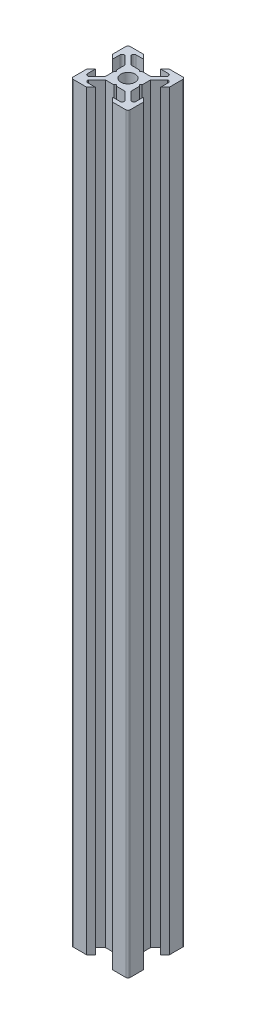
SolidWorks part; units mm, degrees
ref_plane "Face" through (0, 0, 0) normal (0, 0, 1) x (1, 0, 0)
ref_plane "Dessus" through (0, 0, 0) normal (0, 1, 0) x (1, 0, 0)
ref_plane "Droite" through (0, 0, 0) normal (1, 0, 0) x (0, 0, -1)
sketch "Esquisse1" plane through (0, 0, 0) normal (0, 1, 0) x (1, 0, 0)
  line L0 (0, 0) -> (0, 10) construction
  line L1 (0, 0) -> (-10, 0) construction
  line L2 (-10, 0) -> (-10, 10) construction
  line L3 (-10, 10) -> (0, 10) construction
  line L4 (0, 4) -> (-0.5, 4.5)
  line L5 (-0.5, 4.5) -> (-3.4393, 4.5)
  line L6 (-3.4393, 4.5) -> (-6.4393, 7.5)
  line L7 (-6.4393, 7.5) -> (-6.4393, 8.5)
  line L8 (-6.4393, 8.5) -> (-3, 8.5)
  line L9 (-3, 8.5) -> (-4.5, 10)
  line L10 (-4.5, 10) -> (-10, 10)
  line L11 (0, 0) -> (-10, 10) construction
  line L12 (-10, 4.5) -> (-10, 10)
  line L13 (-8.5, 3) -> (-10, 4.5)
  line L14 (-8.5, 6.4393) -> (-8.5, 3)
  line L15 (-7.5, 6.4393) -> (-8.5, 6.4393)
  line L16 (-4.5, 3.4393) -> (-7.5, 6.4393)
  line L17 (-4.5, 0.5) -> (-4.5, 3.4393)
  line L18 (-4, 0) -> (-4.5, 0.5)
  line L19 (0, -4) -> (-0.5, -4.5)
  line L20 (-0.5, -4.5) -> (-3.4393, -4.5)
  line L21 (-4, 0) -> (-4.5, -0.5)
  line L22 (-4.5, -0.5) -> (-4.5, -3.4393)
  line L23 (-4.5, -3.4393) -> (-7.5, -6.4393)
  line L24 (-3.4393, -4.5) -> (-6.4393, -7.5)
  line L25 (-3, -8.5) -> (-4.5, -10)
  line L26 (-6.4393, -8.5) -> (-3, -8.5)
  line L27 (-6.4393, -7.5) -> (-6.4393, -8.5)
  line L28 (-7.5, -6.4393) -> (-8.5, -6.4393)
  line L29 (-4.5, -10) -> (-10, -10)
  line L30 (-10, -4.5) -> (-10, -10)
  line L31 (-8.5, -3) -> (-10, -4.5)
  line L32 (-8.5, -6.4393) -> (-8.5, -3)
  line L33 (8.5, -6.4393) -> (8.5, -3)
  line L34 (8.5, -3) -> (10, -4.5)
  line L35 (10, -4.5) -> (10, -10)
  line L36 (4.5, -10) -> (10, -10)
  line L37 (7.5, -6.4393) -> (8.5, -6.4393)
  line L38 (6.4393, -7.5) -> (6.4393, -8.5)
  line L39 (6.4393, -8.5) -> (3, -8.5)
  line L40 (3, -8.5) -> (4.5, -10)
  line L41 (3.4393, -4.5) -> (6.4393, -7.5)
  line L42 (4.5, -3.4393) -> (7.5, -6.4393)
  line L43 (4.5, -0.5) -> (4.5, -3.4393)
  line L44 (4, 0) -> (4.5, -0.5)
  line L45 (0.5, -4.5) -> (3.4393, -4.5)
  line L46 (0, -4) -> (0.5, -4.5)
  line L47 (4, 0) -> (4.5, 0.5)
  line L48 (4.5, 0.5) -> (4.5, 3.4393)
  line L49 (4.5, 3.4393) -> (7.5, 6.4393)
  line L50 (7.5, 6.4393) -> (8.5, 6.4393)
  line L51 (8.5, 6.4393) -> (8.5, 3)
  line L52 (8.5, 3) -> (10, 4.5)
  line L53 (10, 4.5) -> (10, 10)
  line L54 (4.5, 10) -> (10, 10)
  line L55 (3, 8.5) -> (4.5, 10)
  line L56 (6.4393, 8.5) -> (3, 8.5)
  line L57 (6.4393, 7.5) -> (6.4393, 8.5)
  line L58 (3.4393, 4.5) -> (6.4393, 7.5)
  line L59 (0.5, 4.5) -> (3.4393, 4.5)
  line L60 (0, 4) -> (0.5, 4.5)
  circle A0 centre (0, 0) radius 2.5
  dimension "D10" = 5
  dimension "D1" = 10
  dimension "D2" = 45
  dimension "D3" = 45
  dimension "D4" = 1.5
  dimension "D5" = 7
  dimension "D6" = 1
  dimension "D7" = 4.5
  dimension "D8" = 0.5
  dimension "D9" = 0.75
extrude "Extrusion1" add sketch "Esquisse1" along normal blind 264
fillet "Congé1" radius 0.75 12 edges at (-8.5, 132, -6.4393) (-6.4393, 132, -8.5) (8.5, 132, -6.4393) (6.4393, 132, -8.5) (-8.5, 132, 6.4393) (-6.4393, 132, 8.5) (8.5, 132, 6.4393) (6.4393, 132, 8.5) (10, 132, -10) (-10, 132, -10) (-10, 132, 10) (10, 132, 10)
